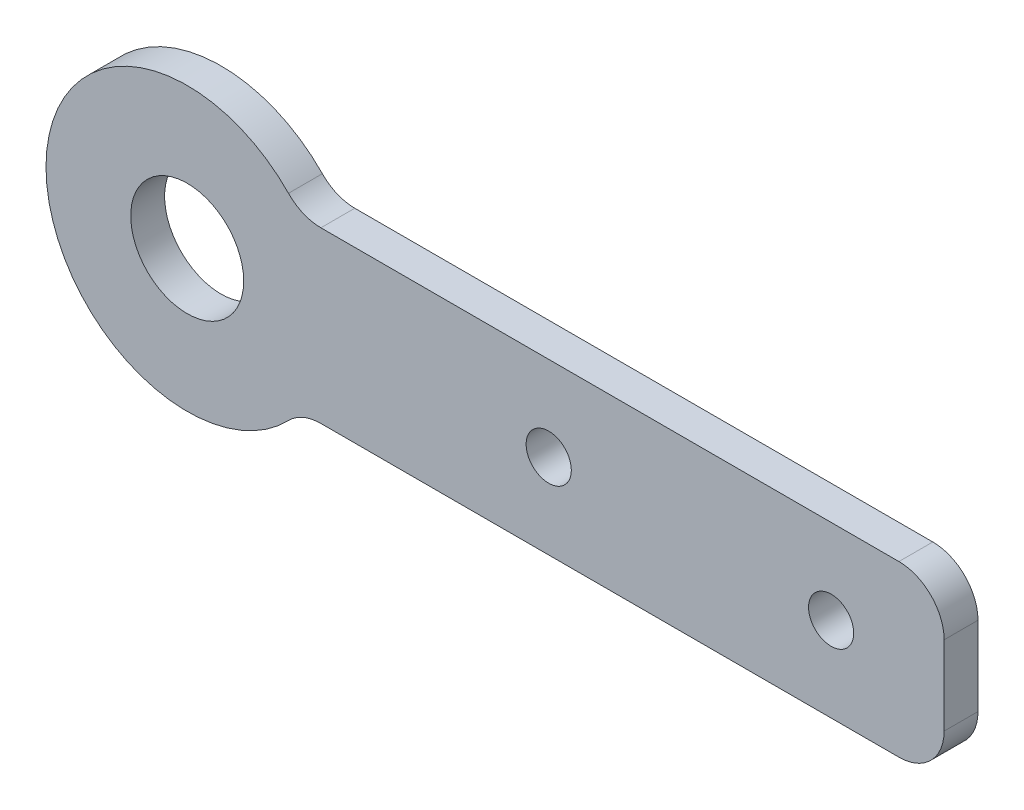
SolidWorks part; units mm, degrees
material "AISI 1020"
ref_plane "Front Plane" through (0, 0, 0) normal (0, 0, 1) x (1, 0, 0)
ref_plane "Top Plane" through (0, 0, 0) normal (0, 1, 0) x (1, 0, 0)
ref_plane "Right Plane" through (0, 0, 0) normal (1, 0, 0) x (0, 0, -1)
sketch "Sketch1" plane through (0, 0, 0) normal (0, 0, 1) x (1, 0, 0)
  line L0 (0, 7.5) -> (77, 7.5) construction
  line L1 (0, 0) -> (77, 0)
  line L2 (0, 0) -> (0, 15)
  line L3 (0, 15) -> (77, 15)
  line L4 (77, 0) -> (77, 15)
  circle A0 centre (10, 7.5) radius 5
  circle A1 centre (42, 7.5) radius 2
  circle A2 centre (67, 7.5) radius 2
  circle A3 centre (10, 7.5) radius 12.5
  dimension "D1" = 10
  dimension "D7" = 4
  dimension "D2" = 25
  dimension "D3" = 32
  dimension "D4" = 10
  dimension "D5" = 10
  dimension "D6" = 15
extrude "Boss-Extrude1" add sketch "Sketch1" along normal blind 3 contours L2 L0 A0 A3 L3 | L3 A3 | L2 A3 | L0 L2 L1 A3 A0 | L1 A3 | L0 A3 L1 L4 A2 A1 | A3 L0 A1 A2 L4 L3
fillet "Fillet2" radius 4 4 edges at (20, 15, 1.5) (77, 0, 1.5) (20, 0, 1.5) (77, 15, 1.5)
